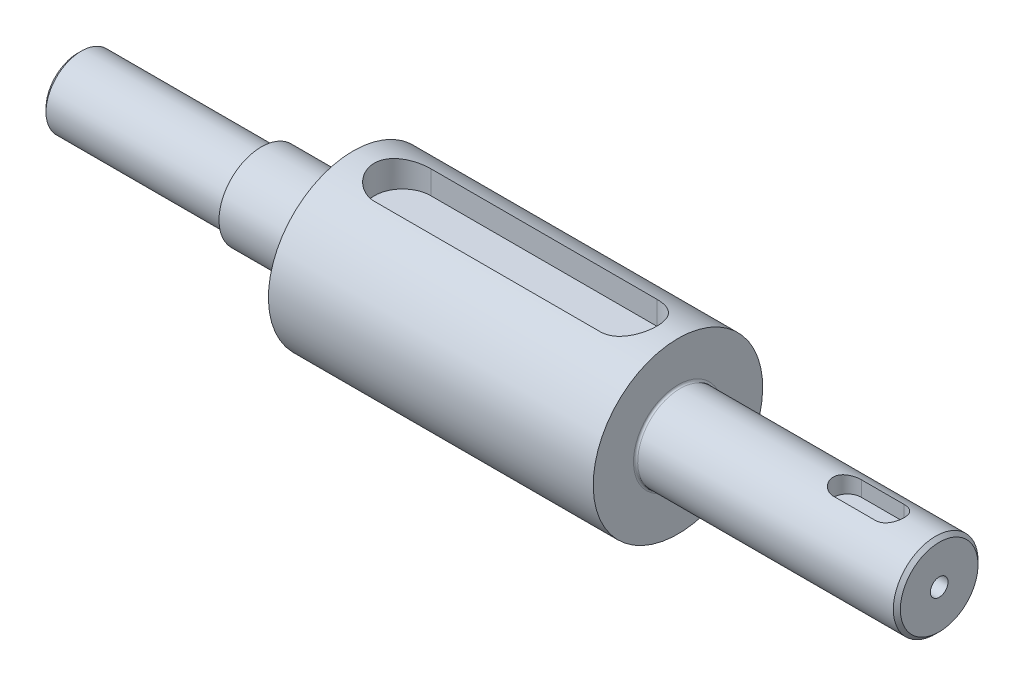
SolidWorks part; units mm, degrees
material "Alloy Steel (SS)"
ref_plane "Front Plane" through (0, 0, 0) normal (0, 0, 1) x (1, 0, 0)
ref_plane "Top Plane" through (0, 0, 0) normal (0, 1, 0) x (1, 0, 0)
ref_plane "Right Plane" through (0, 0, 0) normal (1, 0, 0) x (0, 0, -1)
sketch "Sketch1" plane through (0, 0, 0) normal (0, 0, 1) x (1, 0, 0)
  line L0 (-60, 0) -> (60, 0) construction
  line L6 (26, 6) -> (60, 6)
  line L8 (60, 0) -> (-60, 0)
  line L11 (60, 0) -> (70, 0)
  line L12 (70, 0) -> (70, 6)
  line L13 (70, 6) -> (60, 6)
  line L14 (60, 6) -> (60, 0) construction
  line L16 (23, 12) -> (23, 6)
  line L19 (0, 0) -> (0, 12) construction
  line L25 (-23, 12) -> (23, 12)
  line L27 (-62, 5) -> (-62, 0)
  line L28 (-62, 0) -> (-60, 0)
  line L32 (-36, 6.6) -> (-36, -6.6) construction
  line L33 (-36, 5) -> (-36, 6)
  line L35 (-62, 5) -> (-36, 5)
  line L37 (-36, 6) -> (-23, 6)
  line L38 (23, 6) -> (26, 6)
  line L40 (-23, 6) -> (-23, 12)
  point P3 (-40, 5)
  point P4 (0, 0)
  dimension "D2" = 5
  dimension "D3" = 46
  dimension "D4" = 120
  dimension "D5" = 26
  dimension "D6" = 12
  dimension "D7" = 70
  dimension "D8" = 12
  dimension "D9" = 23
  dimension "D10" = 13
  dimension "D11" = 26
  dimension "D12" = 2
  dimension "D13" = 6
  dimension "D14" = 22
  dimension "D15" = 6
revolve "Revolve1" add sketch "Sketch1" angle 360 about L8
sketch "Sketch2" plane through (0, 0, 0) normal (0, 1, 0) x (1, 0, 0)
  line L0 (-20, 0) -> (20, 0) construction
  line L3 (-16, 0) -> (16, 0) construction
  line L4 (-16, 4) -> (16, 4)
  line L5 (-16, -4) -> (16, -4)
  arc A0 (-16, 4) -> (-16, -4) centre (-16, 0) ccw
  arc A1 (16, -4) -> (16, 4) centre (16, 0) ccw
  point P8 (0, 0)
  dimension "D1" = 8
  dimension "D2" = 32
extrude "Cut-Extrude1" cut sketch "Sketch2" along normal blind 4 from offset 8
sketch "Sketch3" plane through (70, 0, 0) normal (1, 0, 0) x (0, 0, -1)
  line L1 (-4, 4.5) -> (4, 4.5)
  line L2 (-4, 4.5) -> (-4, 9.5)
  line L3 (-4, 9.5) -> (4, 9.5)
  line L4 (4, 4.5) -> (4, 9.5)
  line L5 (-4, 4.5) -> (4, 9.5) construction
  line L6 (-4, 9.5) -> (4, 4.5) construction
  point P0 (0, 7)
  dimension "D1" = 8
  dimension "D2" = 7
  dimension "D3" = 5
extrude "Cut-Extrude2" cut sketch "Sketch3" against normal blind 10
sketch "Sketch4" plane through (0, 4.5, 0) normal (0, 1, 0) x (1, 0, 0)
  line L0 (70, -3.9686) -> (70, 3.9686) construction
  circle A0 centre (65, 0) radius 1.25
  dimension "D1" = 2.5
  dimension "5" = 5
extrude "Cut-Extrude3" cut sketch "Sketch4" against normal blind 4
sketch "Sketch5" plane through (60, 0, 0) normal (1, 0, 0) x (0, 0, -1)
  circle A0 centre (0, 0) radius 6
  dimension "D1" = 12
extrude "Cut-Extrude4" cut sketch "Sketch5" along normal blind 10
sketch "Sketch6" plane through (60, 0, 0) normal (1, 0, 0) x (0, 0, -1)
  point P0 (0, 0)
sketch "Sketch7" plane through (0, 0, 0) normal (0, 1, 0) x (1, 0, 0)
  line L0 (60, 0) -> (0, 0) construction
  line L1 (60, -6) -> (60, 6) construction
  line L2 (47, 0) -> (53, 0) construction
  line L3 (47, 2) -> (53, 2)
  line L4 (47, -2) -> (53, -2)
  arc A0 (47, 2) -> (47, -2) centre (47, 0) ccw
  arc A1 (53, -2) -> (53, 2) centre (53, 0) ccw
  point P7 (50, 0)
  dimension "D1" = 4
  dimension "D2" = 6
  dimension "D3" = 10
extrude "Cut-Extrude5" cut sketch "Sketch7" against normal blind 2.5 from offset 6
hole_wizard "M3 Tapped Hole1" positions "3DSketch2" profile "Sketch10" tap size "M3" standard "ISO"
sketch3d "3DSketch2"
  line L0 (-62, 0, 0) -> (-36, 0, 0) construction
  point P0 (-62, 0, 0)
  point P4 (60, 0, 0)
sketch "Sketch10" plane through (-62, 0, 0) normal (0, 1, 0) x (0, 0, 1)
  line L0 (0, 0) -> (0, 7.5)
  line L1 (0, 7.5) -> (1.25, 6.7489)
  line L2 (1.25, 6.7489) -> (1.25, 0)
  line L5 (1.25, 0) -> (0, 0)
  line L10 (0, 7.5) -> (-1.25, 6.7489) construction
  line L11 (0, -6.35) -> (0, 107.95) construction
  dimension "Tap Drill Dia." = 2.5
  dimension "Tap Drill Depth" = 7.5
  dimension "Drill Angle" = 118
cosmetic thread "Hole Thread1" parameters "D1"=6, "D2"=3
cosmetic thread "Hole Thread2" parameters "D1"=6, "D2"=3
chamfer "Chamfer1" distance 0.5 angle 45 2 edges at (-62, 5, 0) (60, 0, 6)
fillet "Fillet1" radius 0.3 3 edges at (-36, 5, 0) (-23, 6, 0) (23, 6, 0)
sketch "Sketch11" plane through (0, 0, 0) normal (0, 0, 1) x (1, 0, 0)
  line L0 (-23, 0) -> (23, 0) construction
  line L1 (-23, 12) -> (-23, -12) construction
  line L2 (23, -12) -> (23, 12) construction
  point P6 (0, 0)
